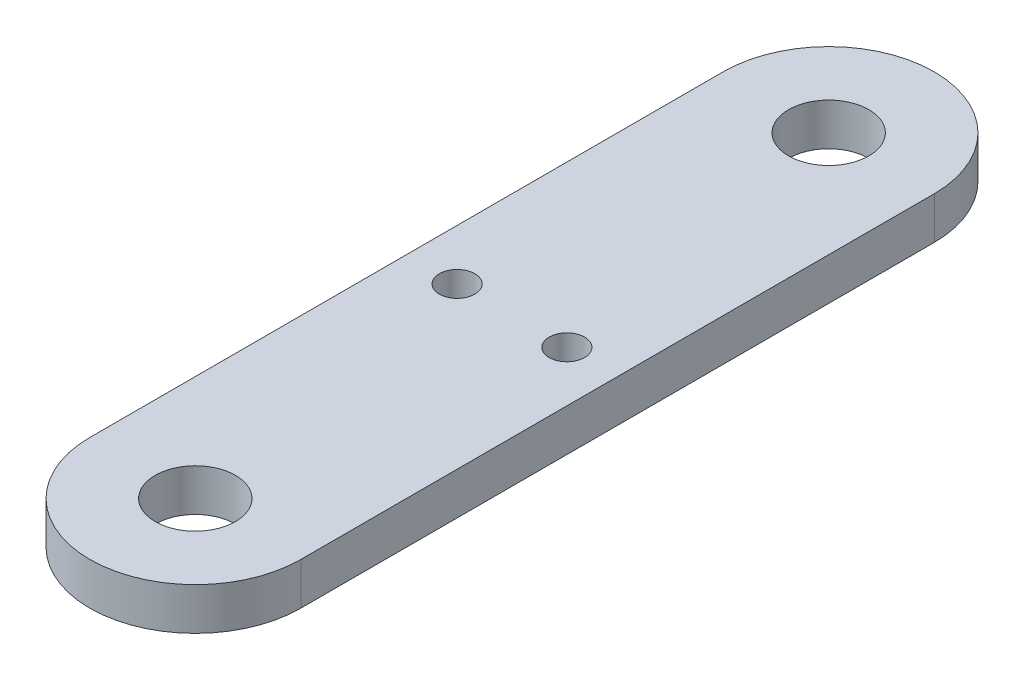
SolidWorks part; units mm, degrees
ref_plane "Front Plane" through (0, 0, 0) normal (0, 0, 1) x (1, 0, 0)
ref_plane "Top Plane" through (0, 0, 0) normal (0, 1, 0) x (1, 0, 0)
ref_plane "Right Plane" through (0, 0, 0) normal (1, 0, 0) x (0, 0, -1)
sketch "Sketch1" plane through (0, 0, 0) normal (0, 1, 0) x (1, 0, 0)
  line L0 (-6.5, 0) -> (6.5, 0) construction
  line L1 (0, 37.5) -> (0, -37.5) construction
  line L2 (12.5, -50) -> (-12.5, -50)
  line L3 (12.5, -50) -> (12.5, 50)
  line L4 (12.5, 50) -> (-12.5, 50)
  line L5 (-12.5, -50) -> (-12.5, 50)
  line L6 (12.5, -50) -> (-12.5, 50) construction
  line L7 (12.5, 50) -> (-12.5, -50) construction
  circle A0 centre (-6.5, 0) radius 2.1
  circle A1 centre (6.5, 0) radius 2.1
  circle A2 centre (0, -37.5) radius 4.75
  circle A3 centre (0, 37.5) radius 4.75
  circle A4 centre (0, 37.5) radius 12.5
  circle A5 centre (0, -37.5) radius 12.5
  point P4 (0, 0)
  dimension "D2" = 4.2
  dimension "D5" = 9.5
  dimension "D1" = 13
  dimension "D3" = 25
  dimension "D4" = 75
extrude "Boss-Extrude1" add sketch "Sketch1" along normal blind 5 contours A4 A3 | A5 L3 A4 L5 A1 A0 | A5 A2
equation "\"m3 hole\"= 3.2"
equation "\"m4 hole\"= 4.2"
equation "\"m5 hole\"= 5.2"
equation "\"m6 hole\"= 6.2"
equation "\"m8 hole\"= 8.2"
equation "\"m3 tapped\"= 2.5"
equation "\"m4 tapped\"= 3.3"
equation "\"m5 tapped\"= 4.2"
equation "\"m6 tapped\"= 5"
equation "\"m8 tapped\"= 6.8"
